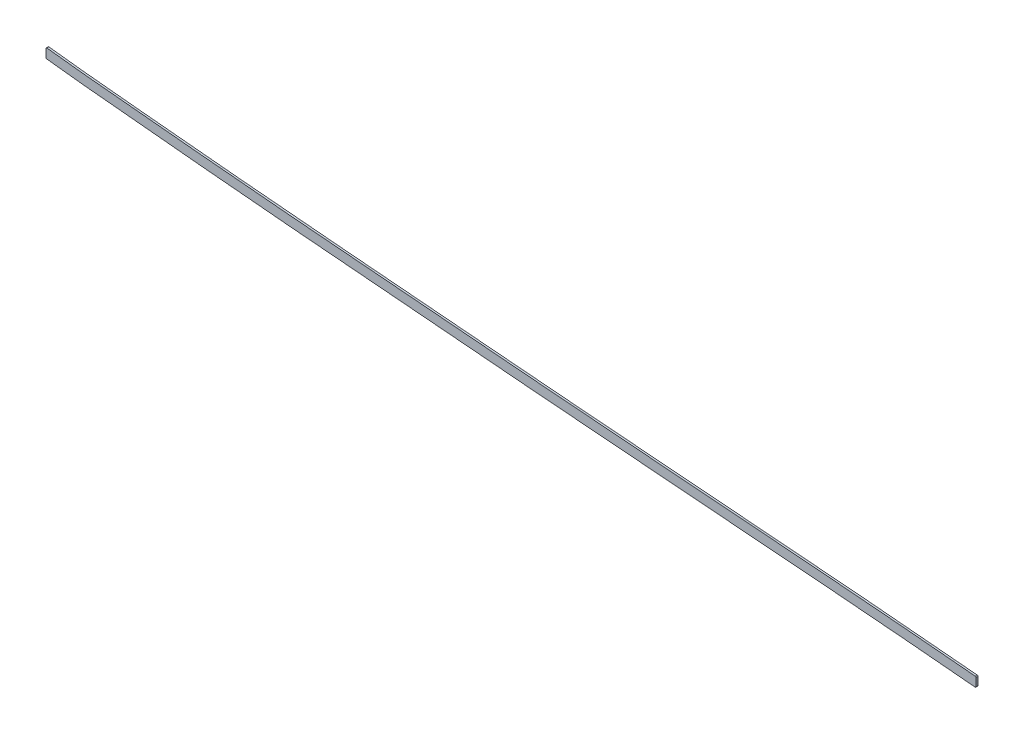
SolidWorks part; units mm, degrees
material "Plywood"
ref_plane "Front Plane" through (0, 0, 0) normal (0, 0, 1) x (1, 0, 0)
ref_plane "Top Plane" through (0, 0, 0) normal (0, 1, 0) x (1, 0, 0)
ref_plane "Right Plane" through (0, 0, 0) normal (1, 0, 0) x (0, 0, -1)
sketch "Sketch2" plane through (0, 0, 0) normal (0, 0, 1) x (1, 0, 0)
  line L0 (0, 0) -> (266.9553, 0) construction
  line L1 (825.5, 263.7287) -> (825.5, 174.6622)
  line L2 (2311.4, 135.8299) -> (2311.4, 52.664)
  spline S0 degree 5 poles (818.067, 264.7065) (827.0431, 263.4992) (836.0291, 262.3734) (845.0868, 261.3058) (891.3865, 256.087) (937.6862, 251.7792) (973.4521, 248.2277) (1071.9467, 239.0511) (1170.4413, 229.7315) (1231.7919, 224.5039) (1324.8993, 216.7906) (1418.0067, 209.0401) (1449.7429, 206.3618) (1636.9286, 190.5211) (1824.1143, 175.4092) (1979.9669, 164.2997) (2156.2686, 150.4144) (2332.5703, 133.8572) (2354.213, 131.7851) (2436.3555, 123.724) (2518.4981, 114.8591) (2579.4813, 107.7425) (2639.6368, 100.3834) (2699.7923, 92.6045) knots 77.930822 77.930822 77.930822 77.930822 77.930822 77.930822 82.465793 82.465793 82.465793 100.79329 100.79329 100.79329 131.098954 131.098954 131.098954 146.769198 146.769198 146.769198 223.533959 223.533959 223.533959 233.943117 233.943117 233.943117 264.216209 264.216209 264.216209 264.216209 264.216209 264.216209 weights 1 1 1 1 1 1 1 1 1 1 1 1 1 1 1 1 1 1 1 1 1 1 1 1
  spline S1 degree 1 poles (816.0355, 249.6025) (2697.8379, 77.4903) knots 0 0 1 1 construction
  spline S2 degree 3 poles (816.0355, 249.6025) (820.896, 248.9488) (830.6112, 247.6997) (845.2811, 245.9534) (860.0865, 244.2956) (879.8307, 242.1866) (904.37, 239.6983) (933.571, 236.8322) (962.6427, 234.0237) (991.7626, 231.242) (1021.072, 228.4759) (1060.3764, 224.797) (1109.513, 220.1844) (1168.5112, 214.8171) (1227.5001, 209.6621) (1306.1332, 203.0212) (1404.3615, 194.9207) (1522.2399, 184.9181) (1640.1829, 175.167) (1758.1654, 165.7576) (1876.1554, 156.5909) (1994.0875, 147.4533) (2092.2687, 139.6242) (2170.748, 133.0797) (2219.7717, 128.8422) (2258.984, 125.3472) (2288.3795, 122.6709) (2317.8122, 119.9317) (2347.5515, 117.1004) (2377.1599, 114.2101) (2406.4697, 111.269) (2435.8183, 108.2401) (2474.9139, 104.0902) (2523.7162, 98.6933) (2582.0419, 91.9123) (2640.0752, 84.8576) (2678.5742, 79.9814) (2697.8379, 77.4903) knots 77.930822 77.930822 77.930822 77.930822 79.386176 80.841531 82.296885 83.75224 86.662949 89.573658 92.484367 95.395077 98.305786 101.216495 107.037913 112.859332 118.68075 124.502168 136.145005 147.787842 159.430678 171.073515 182.716352 194.359189 206.002025 211.823444 217.644862 220.555571 223.46628 226.37699 229.287699 232.198408 235.109117 238.019826 240.930535 246.751954 252.573372 258.39479 264.216209 264.216209 264.216209 264.216209
  spline S3 degree 5 poles (818.067, -264.7065) (827.0431, -263.4992) (836.0291, -262.3734) (845.0868, -261.3058) (891.3865, -256.087) (937.6862, -251.7792) (973.4521, -248.2277) (1071.9467, -239.0511) (1170.4413, -229.7315) (1231.7919, -224.5039) (1324.8993, -216.7906) (1418.0067, -209.0401) (1449.7429, -206.3618) (1636.9286, -190.5211) (1824.1143, -175.4092) (1979.9669, -164.2997) (2156.2686, -150.4144) (2332.5703, -133.8572) (2354.213, -131.7851) (2436.3555, -123.724) (2518.4981, -114.8591) (2579.4813, -107.7425) (2639.6368, -100.3834) (2699.7923, -92.6045) knots 77.930822 77.930822 77.930822 77.930822 77.930822 77.930822 82.465793 82.465793 82.465793 100.79329 100.79329 100.79329 131.098954 131.098954 131.098954 146.769198 146.769198 146.769198 223.533959 223.533959 223.533959 233.943117 233.943117 233.943117 264.216209 264.216209 264.216209 264.216209 264.216209 264.216209 weights 1 1 1 1 1 1 1 1 1 1 1 1 1 1 1 1 1 1 1 1 1 1 1 1
  point P2 (0, 0)
  dimension "D1" = 818.067
  dimension "D2" = 825.5
  dimension "D3" = 2311.4
  dimension "D4" = 15.24
extrude "Boss-Extrude1" add sketch "Sketch2" along normal mid plane 3.175 contours L1 S2 L2 S0
fillet "Fillet1" radius 1.27 4 edges at (2311.4, 120.5233, 0) (825.5, 248.3644, 0)
